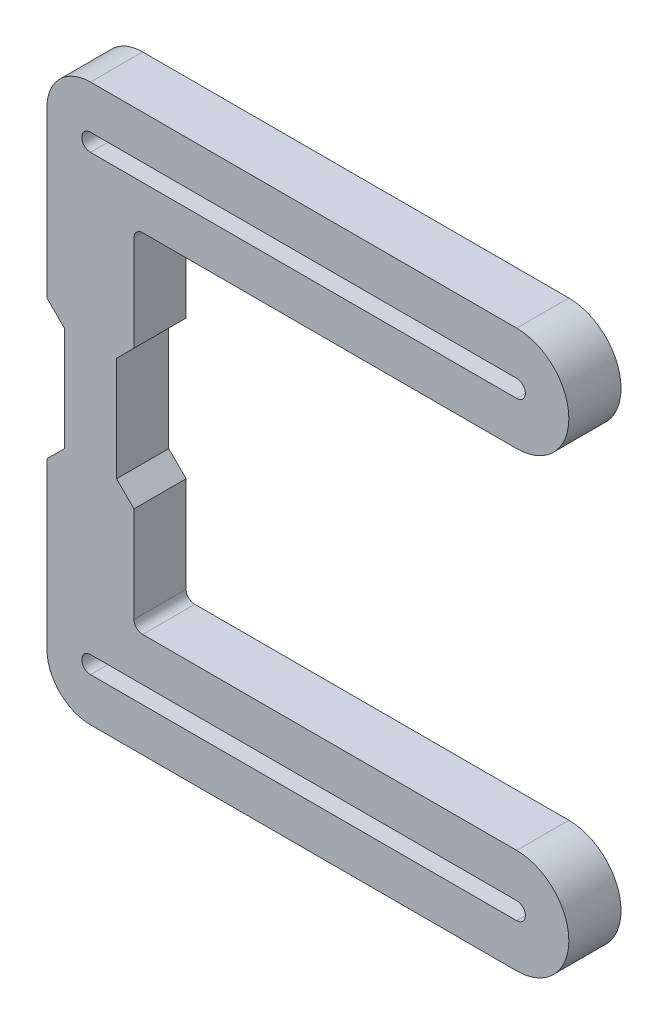
SolidWorks part; units mm, degrees
ref_plane "Front Plane" through (0, 0, 0) normal (0, 0, 1) x (1, 0, 0)
ref_plane "Top Plane" through (0, 0, 0) normal (0, 1, 0) x (1, 0, 0)
ref_plane "Right Plane" through (0, 0, 0) normal (1, 0, 0) x (0, 0, -1)
sketch "Sketch1" plane through (0, 0, 0) normal (0, 0, 1) x (1, 0, 0)
  line L0 (3, 6) -> (5, 8)
  line L1 (5, 8) -> (5, 19)
  line L2 (6, 20) -> (49, 20)
  line L3 (49, 32) -> (0, 32)
  line L4 (-5, 27) -> (-5, 8)
  line L5 (-5, 8) -> (-3, 6)
  line L6 (-3, 6) -> (-3, 0)
  line L7 (-3, 0) -> (3, 0)
  line L8 (3, 0) -> (3, 6)
  line L9 (0, 26) -> (49, 26) construction
  line L10 (0, 27) -> (49, 27)
  line L11 (0, 25) -> (49, 25)
  line L12 (0, 0) -> (0, 42.7689) construction
  arc A0 (49, 20) -> (49, 32) centre (49, 26) ccw
  arc A1 (0, 27) -> (0, 25) centre (0, 26) ccw
  arc A2 (49, 25) -> (49, 27) centre (49, 26) ccw
  arc A3 (0, 32) -> (-5, 27) centre (0, 27) ccw
  arc A4 (6, 20) -> (5, 19) centre (6, 19) ccw
  point P6 (24.5, 26)
  point P14 (55, 26)
  point P15 (3, 3)
  point P25 (5, 20)
  point P26 (53.3931, 30.1385)
  point P27 (0, 0)
  dimension "D7" = 5
  dimension "D8" = 1
  dimension "D1" = 60
  dimension "D2" = 12
  dimension "D3" = 12
  dimension "D4" = 6
  dimension "D5" = 6
  dimension "D6" = 2
  dimension "D9" = 10
  dimension "D10" = 5
extrude "Boss-Extrude1" add sketch "Sketch1" along normal blind 6
mirror "Mirror1" about plane through (-3, 0, 6) normal (0, 1, 0) of "Boss-Extrude1"
